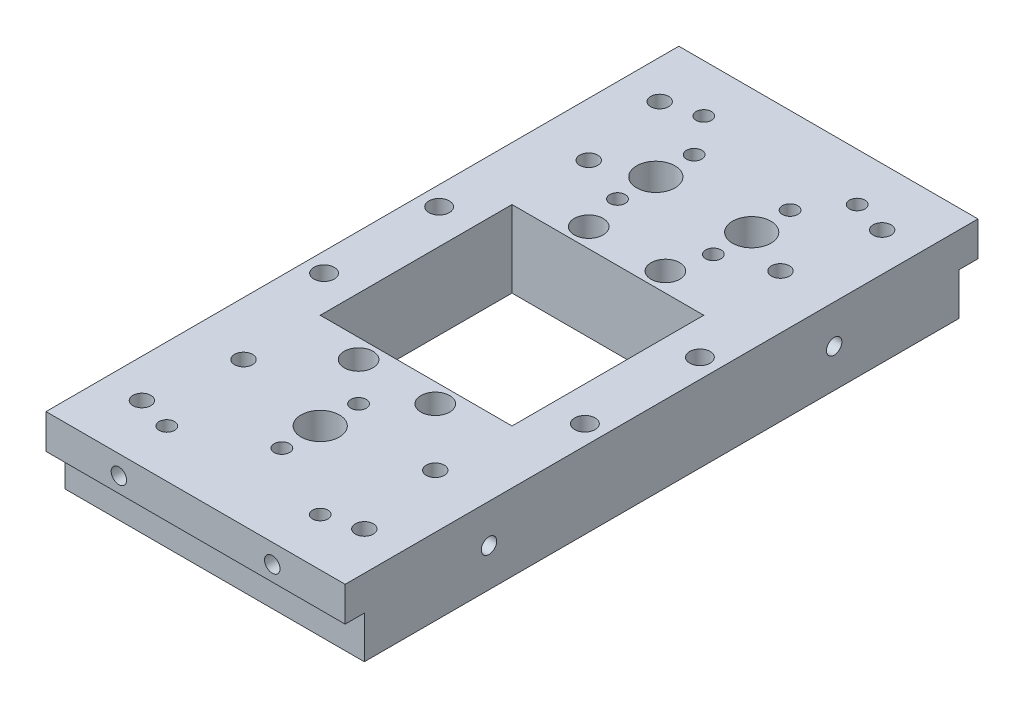
SolidWorks part; units mm, degrees
material "6061 Alloy"
ref_plane "Front Plane" through (0, 0, 0) normal (0, 0, 1) x (1, 0, 0)
ref_plane "Top Plane" through (0, 0, 0) normal (0, 1, 0) x (1, 0, 0)
ref_plane "Right Plane" through (0, 0, 0) normal (1, 0, 0) x (0, 0, -1)
sketch "Sketch1" plane through (0, 0, 0) normal (0, 1, 0) x (1, 0, 0)
  line L1 (-49.53, 104.775) -> (49.53, 104.775)
  line L2 (-49.53, 104.775) -> (-49.53, -104.775)
  line L3 (-49.53, -104.775) -> (49.53, -104.775)
  line L4 (49.53, 104.775) -> (49.53, -104.775)
  dimension "D1" = 49.53
  dimension "D2" = 49.53
  dimension "D3" = 104.775
  dimension "D4" = 104.775
extrude "Boss-Extrude1" add sketch "Sketch1" along normal mid plane 25.4
sketch "Sketch2" plane through (0, 12.7, 0) normal (0, 1, 0) x (1, 0, 0)
  line L1 (-31.75, 31.75) -> (31.75, 31.75)
  line L2 (-31.75, 31.75) -> (-31.75, -31.75)
  line L3 (-31.75, -31.75) -> (31.75, -31.75)
  line L4 (31.75, 31.75) -> (31.75, -31.75)
  dimension "D1" = 31.75
  dimension "D2" = 31.75
  dimension "D3" = 31.75
  dimension "D4" = 31.75
extrude "Cut-Extrude1" cut sketch "Sketch2" against normal blind 25.4
hole_wizard "1/4-20 Tapped Hole1" positions "Sketch5" profile "Sketch4" tap size "1/4-20" standard "ANSI Inch"
sketch "Sketch5" plane through (0, 0, 104.775) normal (0, 0, 1) x (1, 0, 0)
  line L0 (-49.53, 12.7) -> (49.53, 12.7) construction
  point P0 (-25.4, 6.35)
  point P2 (25.4, 6.35)
  dimension "D1" = 25.4
  dimension "D2" = 25.4
  dimension "D3" = 6.35
sketch "Sketch4" plane through (-25.4, 6.35, 104.775) normal (1, 0, 0) x (0, -1, 0)
  line L0 (0, 0) -> (0, 20.5838)
  line L1 (0, 20.5838) -> (2.5527, 19.05)
  line L2 (2.5527, 19.05) -> (2.5527, 0)
  line L5 (2.5527, 0) -> (0, 0)
  line L10 (0, 20.5838) -> (-2.5527, 19.05) construction
  line L11 (0, -6.35) -> (0, 107.95) construction
  dimension "Tap Drill Dia." = 5.1054
  dimension "Tap Drill Depth" = 19.05
  dimension "Drill Angle" = 118
cosmetic thread "Hole Thread1" parameters "D1"=12.7, "D2"=6.35
cosmetic thread "Hole Thread2" parameters "D1"=12.7, "D2"=6.35
hole_wizard "CBORE for 1/4 Socket Head Cap Screw1" positions "Sketch7" profile "Sketch6" counterbore size "1/4" standard "ANSI Inch" end condition through all
sketch "Sketch7" plane through (0, -12.7, 0) normal (0, -1, 0) x (-1, 0, 0)
  point P0 (43.18, 19.05)
  point P2 (43.18, -19.05)
  point P4 (-43.18, -19.05)
  point P6 (-43.18, 19.05)
  dimension "D1" = 19.05
  dimension "D2" = 19.05
  dimension "D3" = 43.18
  dimension "D4" = 43.18
sketch "Sketch6" plane through (-43.18, -12.7, -19.05) normal (1, 0, 0) x (0, 0, -1)
  line L0 (0, 0) -> (0, 25.4)
  line L1 (0, 25.4) -> (3.3782, 25.4)
  line L3 (3.3782, 25.4) -> (3.3782, 6.35)
  line L4 (3.3782, 6.35) -> (5.5562, 6.35)
  line L5 (5.5562, 6.35) -> (5.5562, 0)
  line L7 (5.5562, 0) -> (0, 0)
  line L11 (0, -6.35) -> (0, 107.95) construction
  dimension "Thru Hole Dia." = 6.7564
  dimension "Thru Hole Depth" = 25.4
  dimension "C'Bore Dia." = 11.1125
  dimension "C'Bore Depth" = 6.35
hole_wizard "15/64 (0.23438) Diameter Hole1" positions "Sketch9" profile "Sketch8" hole size "15/64" standard "ANSI Inch" end condition through all
sketch "Sketch9" plane through (0, 12.7, 0) normal (0, 1, 0) x (1, 0, 0)
  line L0 (49.53, -104.775) -> (49.53, 104.775) construction
  line L1 (-49.53, 104.775) -> (-49.53, -104.775) construction
  line L2 (49.53, 104.775) -> (-49.53, 104.775) construction
  line L3 (-49.53, -104.775) -> (49.53, -104.775) construction
  line L4 (31.75, 31.75) -> (-31.75, 31.75) construction
  line L5 (-31.75, -31.75) -> (31.75, -31.75) construction
  point P0 (-36.83, 85.725)
  point P2 (36.83, 85.725)
  point P4 (36.83, -85.725)
  point P6 (-36.83, -85.725)
  point P18 (-31.75, -57.15)
  point P20 (31.75, -57.15)
  point P22 (31.75, 57.15)
  point P24 (-31.75, 57.15)
  dimension "D1" = 12.7
  dimension "D2" = 12.7
  dimension "D3" = 19.05
  dimension "D4" = 19.05
  dimension "D5" = 31.75
  dimension "D6" = 31.75
  dimension "D7" = 25.4
  dimension "D8" = 25.4
sketch "Sketch8" plane through (-36.83, 12.7, -85.725) normal (1, 0, 0) x (0, 0, 1)
  line L0 (0, 0) -> (0, 25.4)
  line L1 (0, 25.4) -> (2.9766, 25.4)
  line L2 (2.9766, 25.4) -> (2.9766, 0)
  line L5 (2.9766, 0) -> (0, 0)
  line L11 (0, -6.35) -> (0, 107.95) construction
  dimension "Thru Hole Dia." = 5.9533
  dimension "Thru Hole Depth" = 25.4
hole_wizard "1/2 (0.5) Diameter Hole1" positions "Sketch11" profile "Sketch10" hole size "1/2" standard "ANSI Inch" end condition up to next
sketch "Sketch11" plane through (0, 12.7, 0) normal (0, 1, 0) x (1, 0, 0)
  point P0 (0, -63.5)
  point P2 (-15.875, 63.5)
  point P4 (15.875, 63.5)
  dimension "D1" = 15.875
  dimension "D2" = 15.875
  dimension "D3" = 63.5
  dimension "D4" = 63.5
sketch "Sketch10" plane through (0, 12.7, 63.5) normal (1, 0, 0) x (0, 0, 1)
  line L0 (0, 0) -> (0, 25.4)
  line L1 (0, 25.4) -> (6.35, 25.4)
  line L2 (6.35, 25.4) -> (6.35, 0)
  line L5 (6.35, 0) -> (0, 0)
  line L11 (0, -6.35) -> (0, 107.95) construction
  dimension "Thru Hole Dia." = 12.7
  dimension "Thru Hole Depth" = 25.4
mirror "Mirror1" about plane through (0, 0, 0) normal (0, 0, 1) of "1/4-20 Tapped Hole1"
hole_wizard "1/4-20 Tapped Hole4" positions "Sketch13" profile "Sketch12" tap size "1/4-20" standard "ANSI Inch"
sketch "Sketch13" plane through (49.53, 0, 0) normal (1, 0, 0) x (0, 0, -1)
  point P0 (-57.15, 0)
  point P2 (57.15, 0)
  dimension "D1" = 57.15
  dimension "D2" = 57.15
sketch "Sketch12" plane through (49.53, 0, 57.15) normal (0, 1, 0) x (0, 0, -1)
  line L0 (0, 0) -> (0, 21.8538)
  line L1 (0, 21.8538) -> (2.5527, 20.32)
  line L2 (2.5527, 20.32) -> (2.5527, 0)
  line L5 (2.5527, 0) -> (0, 0)
  line L10 (0, 21.8538) -> (-2.5527, 20.32) construction
  line L11 (0, -6.35) -> (0, 107.95) construction
  dimension "Tap Drill Dia." = 5.1054
  dimension "Tap Drill Depth" = 20.32
  dimension "Drill Angle" = 118
cosmetic thread "Hole Thread14" parameters "D1"=15.24, "D2"=6.35
cosmetic thread "Hole Thread15" parameters "D1"=15.24, "D2"=6.35
mirror "Mirror2" about plane through (0, 0, 0) normal (1, 0, 0) of "1/4-20 Tapped Hole4"
sketch "Sketch15" plane through (0, 12.7, 0) normal (0, 1, 0) x (1, 0, 0)
  circle A0 centre (12.7, -38.1) radius 4.7625
  circle A1 centre (-12.7, -38.1) radius 4.7625
  dimension "D1" = 12.7
  dimension "D2" = 12.7
  dimension "D3" = 38.1
extrude "Cut-Extrude2" cut sketch "Sketch15" against normal up to next (25.4 mm away)
mirror "Mirror3" about plane through (0, 0, 0) normal (0, 0, 1) of "Cut-Extrude2"
hole_wizard "1/4-20 Tapped Hole5" positions "Sketch17" profile "Sketch16" tap size "1/4-20" standard "ANSI Inch" end condition up to next
sketch "Sketch17" plane through (0, 12.7, 0) normal (0, 1, 0) x (1, 0, 0)
  circle A0 centre (0, -63.5) radius 6.35 construction
  circle A1 centre (15.875, 63.5) radius 6.35 construction
  point P0 (0, -76.2)
  point P2 (0, -50.8)
  point P4 (15.875, 50.8)
  point P6 (15.875, 76.2)
  point P8 (-15.875, 50.8)
  point P10 (-15.875, 76.2)
  dimension "D1" = 12.7
  dimension "D2" = 12.7
  dimension "D3" = 12.7
  dimension "D4" = 12.7
  dimension "D5" = 15.875
  dimension "D6" = 15.875
sketch "Sketch16" plane through (0, 12.7, 76.2) normal (1, 0, 0) x (0, 0, 1)
  line L0 (0, 0) -> (0, 25.4)
  line L1 (0, 25.4) -> (2.5527, 25.4)
  line L2 (2.5527, 25.4) -> (2.5527, 0)
  line L5 (2.5527, 0) -> (0, 0)
  line L11 (0, -6.35) -> (0, 107.95) construction
  dimension "Thru Tap Drill Dia." = 5.1054
  dimension "Thru Tap Drill Depth" = 25.4
cosmetic thread "Hole Thread16" parameters "D2"=6.35
cosmetic thread "Hole Thread17" parameters "D2"=6.35
cosmetic thread "Hole Thread18" parameters "D2"=6.35
cosmetic thread "Hole Thread19" parameters "D2"=6.35
cosmetic thread "Hole Thread20" parameters "D2"=6.35
cosmetic thread "Hole Thread21" parameters "D2"=6.35
hole_wizard "1/4-20 Tapped Hole6" positions "Sketch19" profile "Sketch18" tap size "1/4-20" standard "ANSI Inch" end condition through all
sketch "Sketch19" plane through (0, 12.7, 0) normal (0, 1, 0) x (1, 0, 0)
  line L0 (-49.53, -104.775) -> (49.53, -104.775) construction
  point P0 (-25.4, -88.9)
  point P2 (25.4, -88.9)
  dimension "D1" = 25.4
  dimension "D2" = 25.4
  dimension "D3" = 15.875
sketch "Sketch18" plane through (-25.4, 12.7, 88.9) normal (1, 0, 0) x (0, 0, 1)
  line L0 (0, 0) -> (0, 25.4)
  line L1 (0, 25.4) -> (2.5527, 25.4)
  line L2 (2.5527, 25.4) -> (2.5527, 0)
  line L5 (2.5527, 0) -> (0, 0)
  line L11 (0, -6.35) -> (0, 107.95) construction
  dimension "Thru Tap Drill Dia." = 5.1054
  dimension "Thru Tap Drill Depth" = 25.4
cosmetic thread "Hole Thread22" parameters "D2"=6.35
cosmetic thread "Hole Thread23" parameters "D2"=6.35
mirror "Mirror4" about plane through (0, 0, 0) normal (0, 0, 1) of "1/4-20 Tapped Hole6"
sketch "Sketch20" plane through (49.53, 0, 0) normal (1, 0, 0) x (0, 0, -1)
  line L0 (-104.775, 12.7) -> (104.775, 12.7) construction
  line L1 (-104.775, -12.7) -> (-98.425, -12.7)
  line L2 (-104.775, -12.7) -> (-104.775, 1.27)
  line L3 (-104.775, 1.27) -> (-98.425, 1.27)
  line L4 (-98.425, -12.7) -> (-98.425, 1.27)
  dimension "D1" = 6.35
  dimension "D2" = 11.43
extrude "Cut-Extrude3" cut sketch "Sketch20" against normal up to next (99.06 mm away)
mirror "Mirror5" about plane through (0, 0, 0) normal (0, 0, 1) of "Cut-Extrude3"
